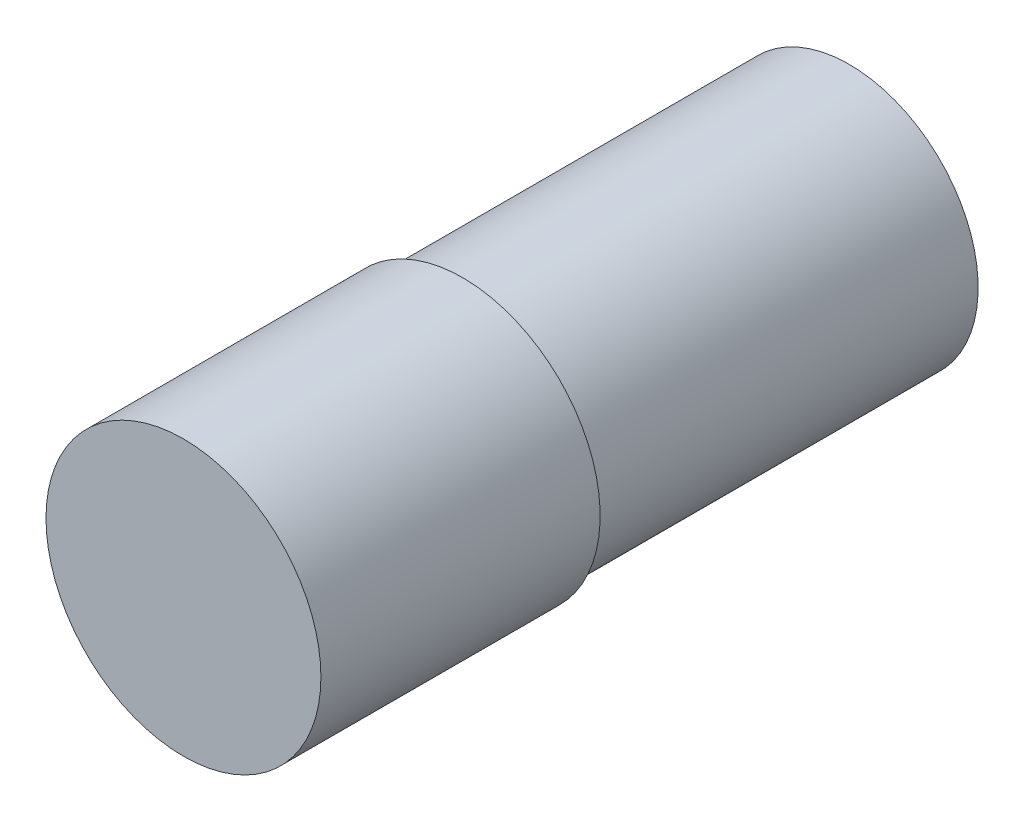
SolidWorks part; units mm, degrees
ref_plane "Front Plane" through (0, 0, 0) normal (0, 0, 1) x (1, 0, 0)
ref_plane "Top Plane" through (0, 0, 0) normal (0, 1, 0) x (1, 0, 0)
ref_plane "Right Plane" through (0, 0, 0) normal (1, 0, 0) x (0, 0, -1)
sketch "Sketch1" plane through (0, 0, 0) normal (0, 0, 1) x (1, 0, 0)
  circle A0 centre (0, 0) radius 3.2
  dimension "D1" = 6.4
extrude "Boss-Extrude1" add sketch "Sketch1" along normal blind 15.5
sketch "Sketch2" plane through (0, 0, 0) normal (0, 0, -1) x (-1, 0, 0)
  circle A0 centre (0, 0) radius 3
  circle A2 centre (0, 0) radius 3.2
  circle A3 centre (0, 0) radius 3.2
  dimension "D1" = 6
  dimension "D2" = 0
extrude "Cut-Extrude1" cut sketch "Sketch2" against normal blind 9
